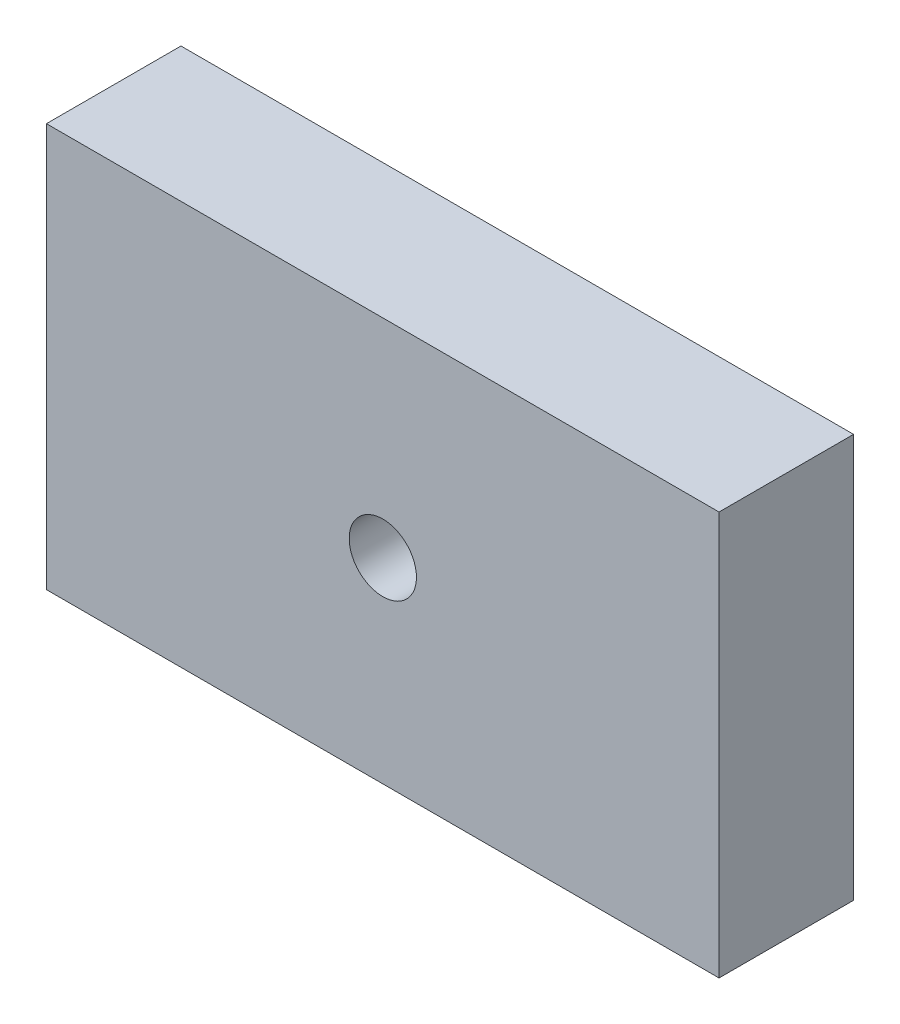
SolidWorks part; units mm, degrees
ref_plane "Front Plane" through (0, 0, 0) normal (0, 0, 1) x (1, 0, 0)
ref_plane "Top Plane" through (0, 0, 0) normal (0, 1, 0) x (1, 0, 0)
ref_plane "Right Plane" through (0, 0, 0) normal (1, 0, 0) x (0, 0, -1)
sketch "Sketch1" plane through (0, 0, 0) normal (0, 0, 1) x (1, 0, 0)
  line L1 (-2.0386, 0) -> (47.9614, 0)
  line L2 (-2.0386, 0) -> (-2.0386, -30)
  line L3 (-2.0386, -30) -> (47.9614, -30)
  line L4 (47.9614, 0) -> (47.9614, -30)
extrude "Boss-Extrude1" add sketch "Sketch1" along normal blind 10
sketch "Sketch2" plane through (0, 0, 10) normal (0, 0, 1) x (1, 0, 0)
  circle A0 centre (22.9681, -15.4481) radius 2.5
extrude "Cut-Extrude1" cut sketch "Sketch2" against normal blind 10
